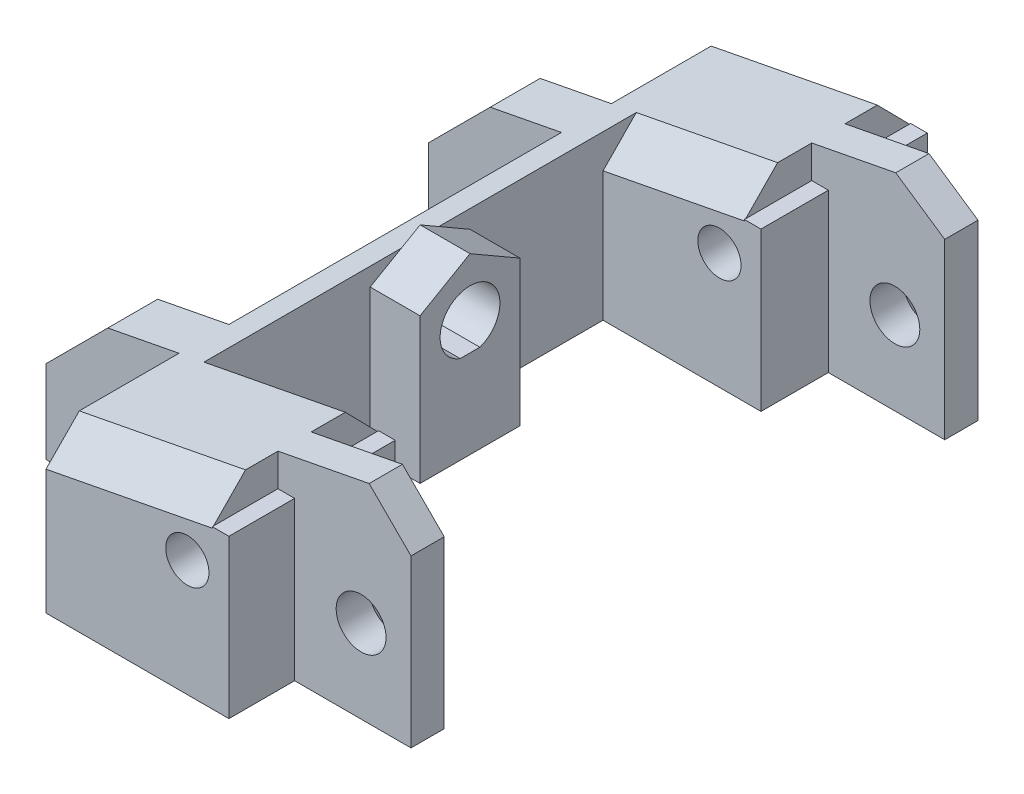
SolidWorks part; units mm, degrees
material "ABS"
ref_plane "前视基准面" through (0, 0, 0) normal (0, 0, 1) x (1, 0, 0)
ref_plane "上视基准面" through (0, 0, 0) normal (0, 1, 0) x (1, 0, 0)
ref_plane "右视基准面" through (0, 0, 0) normal (1, 0, 0) x (0, 0, -1)
sketch "草图1" plane through (0, 0, 0) normal (0, 1, 0) x (1, 0, 0)
  line L0 (5, -17.05) -> (13, -17.05)
  line L1 (5, -21) -> (-5, -21)
  line L2 (5, -21) -> (5, -11)
  line L3 (5, 21) -> (-5, 21)
  line L4 (-5, -21) -> (-5, 21)
  line L5 (5, -21) -> (-5, 21) construction
  line L6 (5, 21) -> (-5, -21) construction
  line L7 (3.5, -11) -> (-3.5, -11)
  line L8 (-15.3944, 0) -> (11.4757, 0) construction
  line L9 (5, 11) -> (5, 21)
  line L10 (3.5, 11) -> (-3.5, 11)
  line L11 (-3.5, -11) -> (-3.5, 11)
  line L12 (3.5, -11) -> (-3.5, 11) construction
  line L13 (3.5, 11) -> (-3.5, -11) construction
  line L14 (13, -17.05) -> (13, -15.05)
  line L15 (13, -15.05) -> (5, -15.05)
  line L16 (5, 17.05) -> (13, 17.05)
  line L17 (13, 17.05) -> (13, 15.05)
  line L18 (13, 15.05) -> (5, 15.05)
  line L19 (0, 10.7263) -> (0, -12.0299) construction
  line L20 (-13, -13) -> (-13, -10)
  line L21 (-5, 13) -> (-13, 13)
  line L22 (-5, 13) -> (-5, 10)
  line L23 (-5, 10) -> (-13, 10)
  line L24 (-13, 13) -> (-13, 10)
  line L25 (-5, -10) -> (-13, -10)
  line L26 (-5, -13) -> (-5, -10)
  line L27 (-5, -13) -> (-13, -13)
  line L28 (3.5, 11) -> (5, 11)
  line L29 (3.5, -11) -> (5, -11)
  line L30 (5, -15.05) -> (5, -17.05)
  line L31 (5, 17.05) -> (5, 15.05)
  point P0 (0, 0)
  point P6 (0, 0)
  dimension "D1" = 42
  dimension "D2" = 7
  dimension "D3" = 10
  dimension "D4" = 2
  dimension "D5" = 8
  dimension "D6" = 15.05
  dimension "D7" = 3
  dimension "D8" = 8
  dimension "D9" = 10
  dimension "D10" = 10
extrude "凸台-拉伸1" add sketch "草图1" along normal blind 13
sketch "草图2" plane through (0, 0, 21) normal (0, 0, 1) x (1, 0, 0)
  line L1 (5, 0) -> (13, 0) construction
  line L2 (5, 13) -> (5, 0) construction
  line L3 (-5, 13) -> (-5, 0) construction
  line L4 (-5, 0) -> (-13, 0) construction
  line L5 (5, 0) -> (-5, 0) construction
  line L6 (-13, 7.9897) -> (13, 13)
  line L8 (-13, 7.9897) -> (-13, 13)
  line L9 (-13, 13) -> (13, 13)
  line L10 (5, 13) -> (5, 0) construction
  circle A0 centre (10, 5) radius 1.5
  circle A1 centre (-8, 2.5) radius 1.5
  circle A2 centre (3.5, 7) radius 1.3
  dimension "D1" = 3
  dimension "D2" = 3
  dimension "D7" = 2.6
  dimension "D3" = 5
  dimension "D4" = 5
  dimension "D5" = 3
  dimension "D6" = 2.5
  dimension "D8" = 7
  dimension "D9" = 1.5
extrude "切除-拉伸1" cut sketch "草图2" against normal through all
chamfer "倒角1" distance 3 angle 45 4 edges at (13, 13, -16.05) (13, 13, 16.05) (-13, 7.9897, -11.5) (-13, 7.9897, 11.5)
chamfer "倒角2" distance 2 angle 45 4 edges at (0, 10.4949, -21) (0.75, 10.6394, -11) (0.75, 10.6394, 11) (0, 10.4949, 21)
sketch "草图3" plane through (0, 0, 0) normal (0, -1, 0) x (1, 0, 0)
  line L1 (5, -21) -> (13.853, -21)
  line L2 (5, -21) -> (5, 21.0016)
  line L3 (5, 21.0016) -> (13.853, 21.0016)
  line L4 (13.853, -21) -> (13.853, 21.0016)
sketch "草图5" plane through (-3.5, 0, 0) normal (1, 0, 0) x (0, 0, -1)
  line L1 (0, 10.4687) -> (-3.004, 8.7343)
  line L2 (-3.004, 8.7343) -> (-3.004, 5.2657)
  line L3 (-3.004, 5.2657) -> (0, 3.5313)
  line L4 (0, 3.5313) -> (3.004, 5.2657)
  line L5 (3.004, 5.2657) -> (3.004, 8.7343)
  line L6 (3.004, 8.7343) -> (0, 10.4687)
  circle A0 centre (0, 7) radius 3.004 construction
  circle A1 centre (0, 7) radius 1.8
extrude "凸台-拉伸2" add sketch "草图5" along normal blind 3
sketch "草图6" plane through (-3.5, 0, 0) normal (1, 0, 0) x (0, 0, -1)
  circle A0 centre (0, 7) radius 1.8
extrude "切除-拉伸2" cut sketch "草图6" against normal blind 3
sketch "草图7" plane through (0, 0, 0) normal (0, -1, 0) x (1, 0, 0)
  line L1 (-3.5, 3.004) -> (-0.5, 3.004)
  line L2 (-3.5, 3.004) -> (-3.5, -3.004)
  line L3 (-3.5, -3.004) -> (-0.5, -3.004)
  line L4 (-0.5, 3.004) -> (-0.5, -3.004)
extrude "凸台-拉伸3" add sketch "草图7" against normal blind 5.3
sketch "草图8" plane through (0, 0, 0) normal (0, -1, 0) x (1, 0, 0)
  line L0 (-20.4846, 0) -> (-6.116, 0) construction
  line L1 (-15.3944, 0) -> (11.4757, 0) construction
  line L2 (6.5, 11) -> (0.5, 11) construction
  line L3 (5, 21) -> (6, 21)
  line L4 (5, 21) -> (5, 11)
  line L5 (5, 11) -> (6, 11)
  line L6 (6, 21) -> (6, 11)
  line L7 (6, -21) -> (6, -11)
  line L8 (5, -11) -> (6, -11)
  line L9 (5, -21) -> (5, -11)
  line L10 (5, -21) -> (6, -21)
  dimension "D1" = 1
extrude "凸台-拉伸4" add sketch "草图8" against normal blind 9.5
